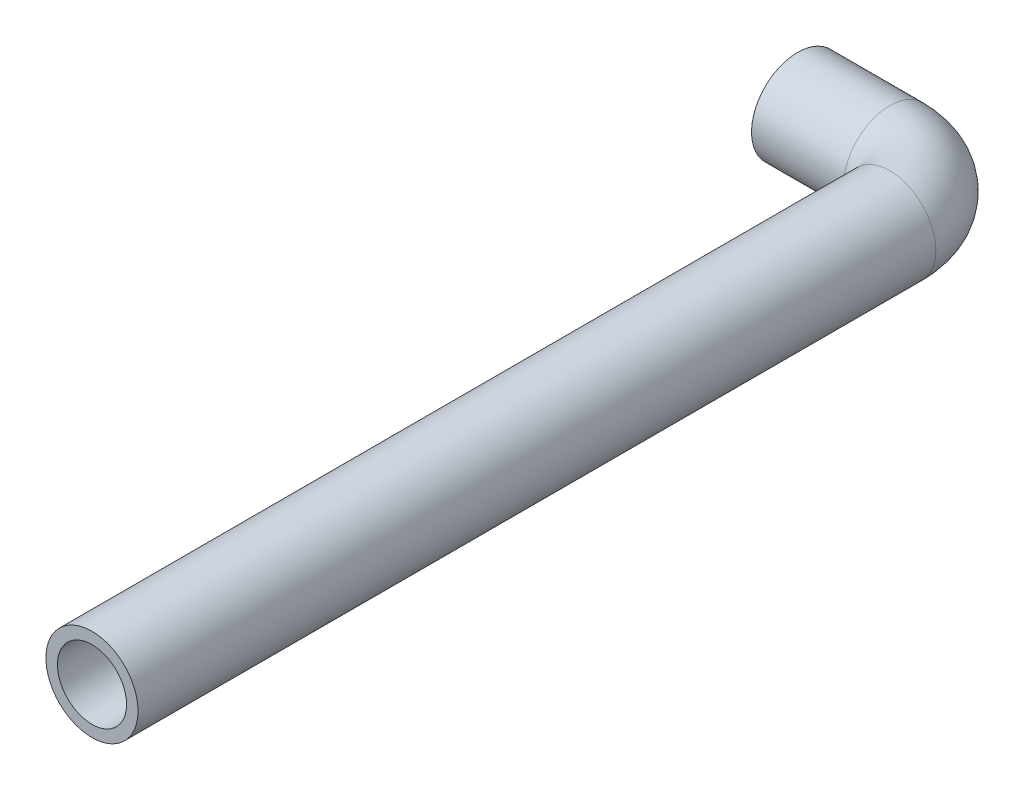
SolidWorks part; units mm, degrees
material "Nylon 101"
ref_plane "Front Plane" through (0, 0, 0) normal (0, 0, 1) x (1, 0, 0)
ref_plane "Top Plane" through (0, 0, 0) normal (0, 1, 0) x (1, 0, 0)
ref_plane "Right Plane" through (0, 0, 0) normal (1, 0, 0) x (0, 0, -1)
sketch "Sketch10" plane through (0, 0, 0) normal (0, 1, 0) x (1, 0, 0)
  line L0 (20.4749, -106.5557) -> (20.4749, 3.4098)
  line L1 (12.7, 11.1847) -> (0, 11.1847)
  line L2 (0, -6.985) -> (0, 6.985) construction
  arc A0 (20.4749, 3.4098) -> (12.7, 11.1847) centre (12.7, 3.4098) ccw
  point P9 (0, 11.1847)
  dimension "D1" = 12.7
sketch "Sketch11" plane through (0, 0, 0) normal (1, 0, 0) x (0, 0, -1)
  circle A0 centre (11.1847, 0) radius 6.35
  circle A1 centre (11.1847, 0) radius 4.7625
  dimension "D1" = 12.7
  dimension "D2" = 9.525
sweep "Sweep4" add profiles "Sketch11" path "Sketch10"
